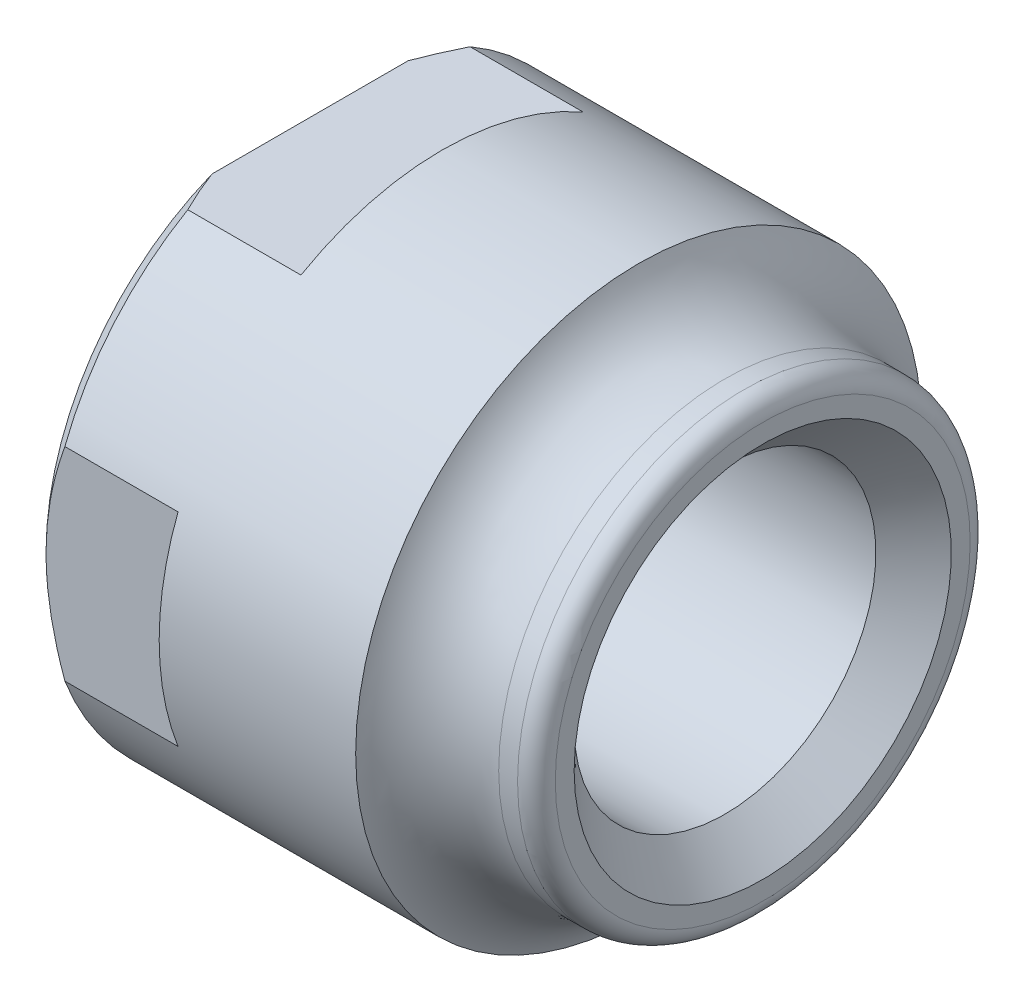
SolidWorks part; units mm, degrees
ref_plane "Plan de face" through (0, 0, 0) normal (0, 0, 1) x (1, 0, 0)
ref_plane "Plan de dessus" through (0, 0, 0) normal (0, 1, 0) x (1, 0, 0)
ref_plane "Plan de droite" through (0, 0, 0) normal (1, 0, 0) x (0, 0, -1)
sketch "Esquisse1" plane through (0, 0, 0) normal (0, 0, 1) x (1, 0, 0)
  line L0 (-14.5399, 0) -> (2.6566, 0) construction
  line L1 (0, 6) -> (1, 6)
  line L2 (-11, 7.5) -> (-2.2913, 7.5)
  line L3 (-11, 7.5) -> (-11, 4)
  line L4 (-11, 4) -> (1, 4)
  line L5 (1, 6) -> (1, 4)
  arc A0 (-2.2913, 7.5) -> (0, 6) centre (0, 8.5) ccw
  dimension "D1" = 5
  dimension "D2" = 8
  dimension "D3" = 17
  dimension "D4" = 12
  dimension "D5" = 15
  dimension "D6" = 1
revolve "Révolution1" add sketch "Esquisse1" angle 360 about L0
fillet "Congé1" radius 0.5 1 edges at (1, 0, 6)
chamfer "Chanfrein1" distance 1 angle 45 2 edges at (1, 0, 4) (-11, 0, 4)
chamfer "Chanfrein2" distance 0.5 angle 45 1 edges at (-11, 0, 7.5)
sketch "Esquisse2" plane through (-11, 0, 0) normal (-1, 0, 0) x (0, 0, 1)
  line L0 (0, 0) -> (0, 3.3951) construction
  line L1 (-7, -6.5) -> (7, -6.5)
  line L2 (-7, -6.5) -> (-7, 6.5)
  line L3 (-7, 6.5) -> (7, 6.5)
  line L4 (7, -6.5) -> (7, 6.5)
  line L5 (0, 0) -> (2.6602, 0) construction
  dimension "D1" = 14
  dimension "D2" = 13
extrude "Enlèv. mat.-Extru.1" cut sketch "Esquisse2" against normal blind 3.5 flip side to cut
